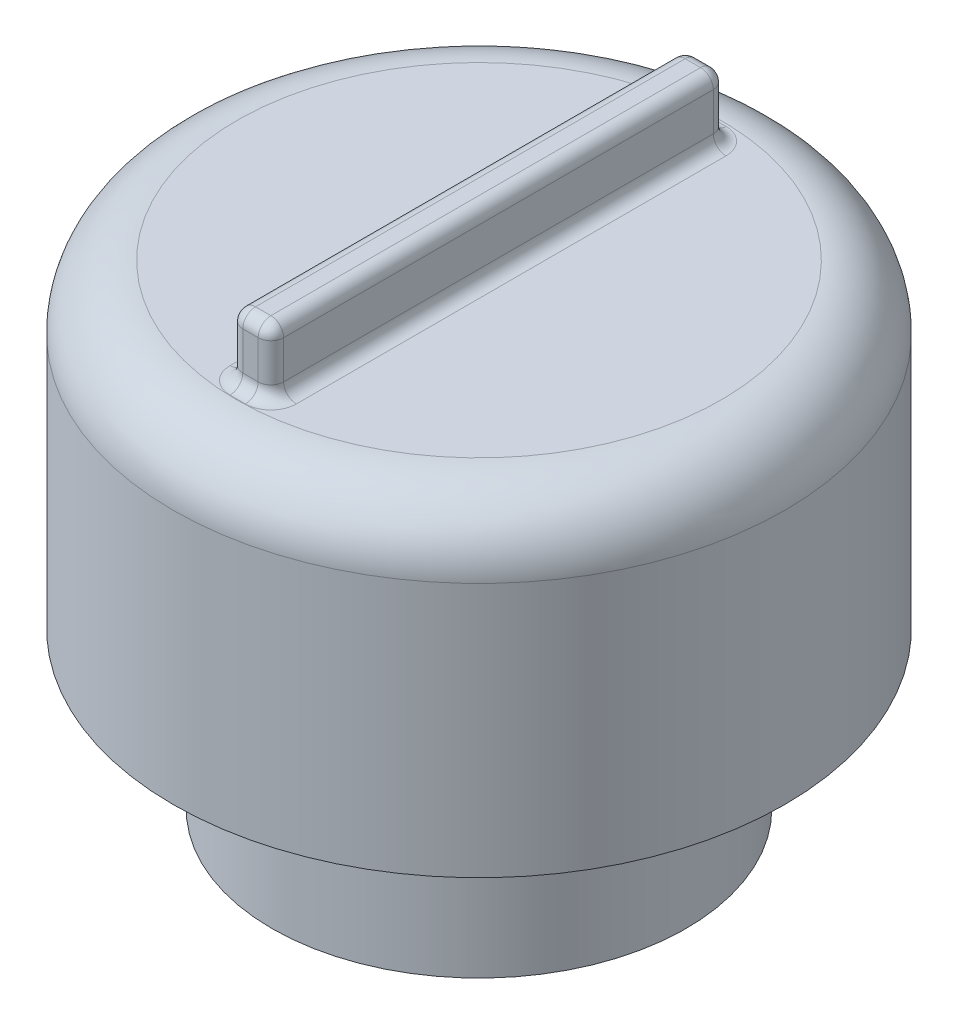
SolidWorks part; units mm, degrees
ref_plane "Front Plane" through (0, 0, 0) normal (0, 0, 1) x (1, 0, 0)
ref_plane "Top Plane" through (0, 0, 0) normal (0, 1, 0) x (1, 0, 0)
ref_plane "Right Plane" through (0, 0, 0) normal (1, 0, 0) x (0, 0, -1)
sketch "Sketch1" plane through (0, 0, 0) normal (0, 1, 0) x (1, 0, 0)
  circle A0 centre (0, 0) radius 3.25
  dimension "D1" = 6.5
extrude "Boss-Extrude1" add sketch "Sketch1" along normal blind 2.46 contours A0
sketch "Sketch2" plane through (0, 0, 0) normal (0, -1, 0) x (1, 0, 0)
  circle A1 centre (0, 0) radius 1.75
  dimension "D1" = 3.5
extrude "Cut-Extrude1" cut sketch "Sketch2" against normal blind 2.5
sketch "Sketch6" plane through (0, 2.46, 0) normal (0, 1, 0) x (1, 0, 0)
  circle A0 centre (0, 0) radius 4.8
  dimension "D1" = 9.6
extrude "Boss-Extrude2" add sketch "Sketch6" along normal blind 5 contours A0
sketch "Sketch10" plane through (0, 7.46, 0) normal (0, 1, 0) x (1, 0, 0)
  line L0 (0, 0) -> (-3.4834, -3.5869) construction
  line L1 (-3.4834, 3.5869) -> (3.4834, 3.5869)
  line L2 (-3.4834, 3.5869) -> (-3.4834, -3.5869)
  line L3 (-3.4834, -3.5869) -> (3.4834, -3.5869)
  line L4 (3.4834, 3.5869) -> (3.4834, -3.5869)
  line L5 (-3.4834, 3.5869) -> (3.4834, -3.5869) construction
  line L6 (-3.4834, -3.5869) -> (3.4834, 3.5869) construction
  point P0 (0, 0)
  dimension "D1" = 10
  dimension "D2" = 3.4834
sketch "Sketch11" plane through (0, 7.46, 0) normal (0, 1, 0) x (1, 0, 0)
  text T0 "I" font "Century Gothic" height in points 27
extrude "Boss-Extrude4" add sketch "Sketch11" along normal blind 1
fillet "Fillet1" radius 0.2 12 edges at (0, 7.46, -3.5569) (-0.3206, 7.96, 3.5869) (0, 7.46, 3.5869) (0.3206, 7.96, 3.5869) (0.3206, 7.96, -3.5569) (0.3206, 7.46, 0.015) (0, 8.46, -3.5569) (0.3206, 8.46, 0.015) (0, 8.46, 3.5869) (-0.3206, 8.46, 0.015) (-0.3206, 7.96, -3.5569) (-0.3206, 7.46, 0.015)
fillet "Fillet2" radius 1 1 edges at (0, 7.46, 4.8)
